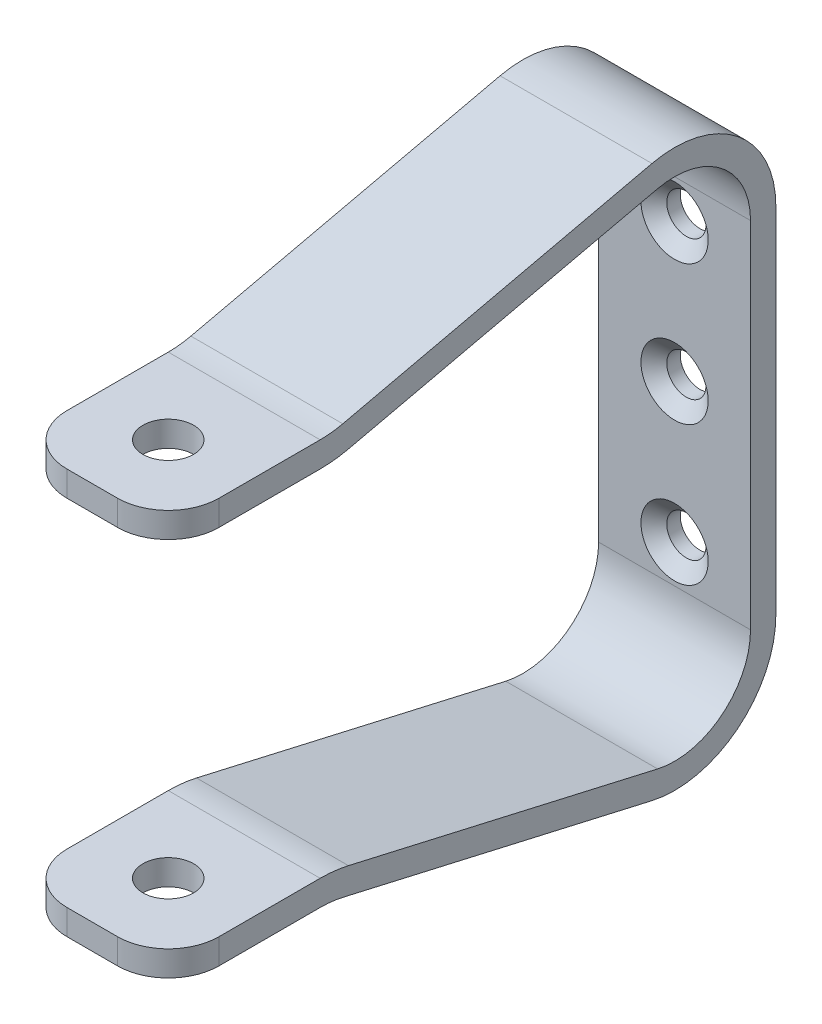
SolidWorks part; units mm, degrees
material "6061 Alloy"
ref_plane "Front Plane" through (0, 0, 0) normal (0, 0, 1) x (1, 0, 0)
ref_plane "Top Plane" through (0, 0, 0) normal (0, 1, 0) x (1, 0, 0)
ref_plane "Right Plane" through (0, 0, 0) normal (1, 0, 0) x (0, 0, -1)
sketch "Sketch2" plane through (0, 0, 66.675) normal (1, 0, 0) x (0, -1, 0)
  line L0 (-34.6043, 51.139) -> (-25.7207, 12.361)
  line L1 (-22.225, 66.675) -> (22.225, 66.675) construction
  line L2 (-22.225, 66.675) -> (22.225, 66.675)
  line L3 (-25.4, 9.525) -> (-25.4, -9.525)
  arc A0 (-22.225, 66.675) -> (-34.6043, 51.139) centre (-22.225, 53.975) ccw
  arc A1 (-25.7207, 12.361) -> (-25.4, 9.525) centre (-38.1, 9.525) cw
  dimension "D4" = 12.7
  dimension "D5" = 12.7
  dimension "D1" = 19.05
  dimension "D2" = 9.525
  dimension "D3" = 25.4
extrude "Extrude-Thin1" add sketch "Sketch2" along normal mid plane 19.05 thin contours L2 A0 L0 A1 L3 thin type one direction reverse wall 3.175
mirror "Mirror1" about plane through (0, 0, 0) normal (0, 1, 0) of "Extrude-Thin1"
sketch "Sketch4" plane through (0, -25.4, 0) normal (0, -1, 0) x (1, 0, 0)
  line L0 (9.525, 76.2) -> (-9.525, 76.2) construction
  circle A0 centre (0, 66.675) radius 3.175
  dimension "D1" = 6.35
  dimension "D2" = 9.525
extrude "Cut-Extrude1" cut sketch "Sketch4" against normal through all
sketch "Sketch5" plane through (0, 0, 3.175) normal (0, 0, 1) x (1, 0, 0)
  circle A0 centre (0, -17.4625) radius 0.889 construction
  circle A1 centre (0, 0) radius 0.889 construction
  circle A2 centre (0, 17.4625) radius 0.889 construction
  circle A3 centre (0, -17.4625) radius 0.889
  circle A4 centre (0, 0) radius 0.889
  circle A5 centre (0, 17.4625) radius 0.889
hole_wizard "CSK for #8 Flat Head Machine Screw (100)1" positions "3DSketch1" profile "Sketch6" countersink size "#8" standard "ANSI Inch" end condition through all
sketch3d "3DSketch1"
  point P0 (0, -17.4625, 3.175)
  point P3 (0, 0, 3.175)
  point P6 (0, 17.4625, 3.175)
sketch "Sketch6" plane through (0, -17.4625, 3.175) normal (1, 0, 0) x (0, -1, 0)
  line L0 (0, 0) -> (0, 3.175)
  line L1 (0, 3.175) -> (2.4574, 3.175)
  line L2 (2.4574, 3.175) -> (2.4574, 1.4759)
  line L3 (2.4574, 1.4759) -> (4.2164, 0)
  line L5 (4.2164, 0) -> (0, 0)
  line L6 (-2.4574, 1.4759) -> (-4.2164, 0) construction
  line L11 (0, -6.35) -> (0, 107.95) construction
  dimension "Thru Hole Dia." = 4.9149
  dimension "Thru Hole Depth" = 3.175
  dimension "Near C'Sink Dia." = 8.4328
  dimension "Near C'Sink Angle" = 100
fillet "Fillet1" radius 6.35 4 edges at (9.525, 23.8125, 76.2) (-9.525, 23.8125, 76.2) (-9.525, -23.8125, 76.2) (9.525, -23.8125, 76.2)
equation "\"D2@Sketch2\"=\"D1@Sketch2\"/2"
